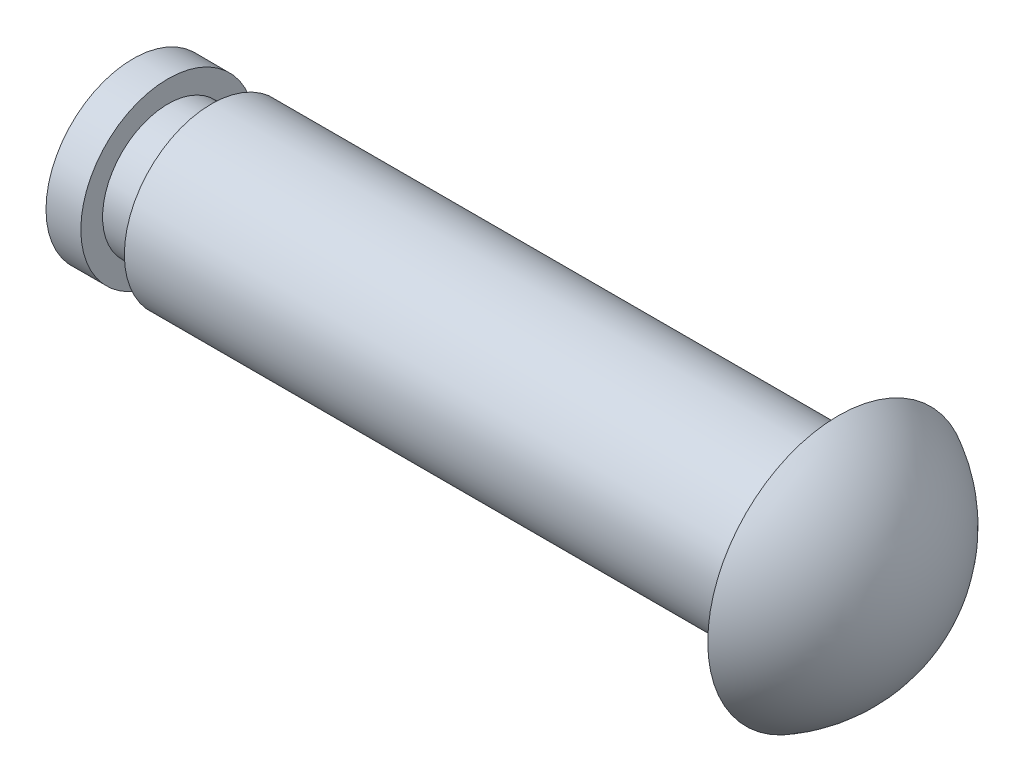
SolidWorks part; units mm, degrees
material "Plain Carbon Steel"
ref_plane "Front Plane" through (0, 0, 0) normal (0, 0, 1) x (1, 0, 0)
ref_plane "Top Plane" through (0, 0, 0) normal (0, 1, 0) x (1, 0, 0)
ref_plane "Right Plane" through (0, 0, 0) normal (1, 0, 0) x (0, 0, -1)
sketch "Sketch1" plane through (0, 0, 0) normal (0, 0, 1) x (1, 0, 0)
  line L0 (0, 0) -> (34.4, 0) construction
  line L1 (0, 4) -> (34.4, 4)
  line L2 (0, 0) -> (0, 4)
  line L3 (34.4, 4) -> (34.4, 6)
  line L4 (34.4, 0) -> (38, 0) construction
  line L5 (0, 0) -> (38, 0)
  arc A0 (38, 0) -> (34.4, 6) centre (31.2, 0) ccw
  dimension "D1" = 34.4
  dimension "D2" = 4
  dimension "D3" = 2
  dimension "D4" = 38
revolve "Revolve1" add sketch "Sketch1" angle 360 about L5
sketch "Sketch2" plane through (0, 0, 0) normal (0, 1, 0) x (1, 0, 0)
  line L1 (34.4, 0) -> (5.6, 0) construction
  line L2 (34.4, 4) -> (34.4, -4) construction
  circle A0 centre (4.6, 0) radius 1
  dimension "D1" = 2
  dimension "D2" = 28.8
extrude "Cut-Extrude1" cut sketch "Sketch2" against normal through all both and the other way through all
sketch "Sketch3" plane through (0, 0, 0) normal (0, 1, 0) x (1, 0, 0)
  line L0 (34.4, 0) -> (5.6, 0) construction
  line L1 (34.4, 4) -> (34.4, -4) construction
  line L2 (34.4, 4) -> (0, 4) construction
  line L3 (3.6, 4) -> (5.6, 4)
  line L4 (3.6, 4) -> (3.6, 3)
  line L5 (3.6, 3) -> (5.6, 3)
  line L6 (5.6, 4) -> (5.6, 3)
  dimension "D1" = 2
  dimension "D2" = 1
  dimension "D3" = 28.8
revolve "Cut-Revolve1" cut sketch "Sketch3" angle 360 about L0
sketch "Sketch4" plane through (0, 0, 0) normal (-1, 0, 0) x (0, 0, 1)
  circle A0 centre (0, 0) radius 4
extrude "Cut-Extrude2" cut sketch "Sketch4" against normal blind 2
sketch "Sketch5" plane through (2, 0, 0) normal (-1, 0, 0) x (0, 0, 1)
  circle A0 centre (0, 0) radius 3
  dimension "D1" = 6
extrude "Boss-Extrude1" add sketch "Sketch5" against normal up to vertex (32.4 mm away)
